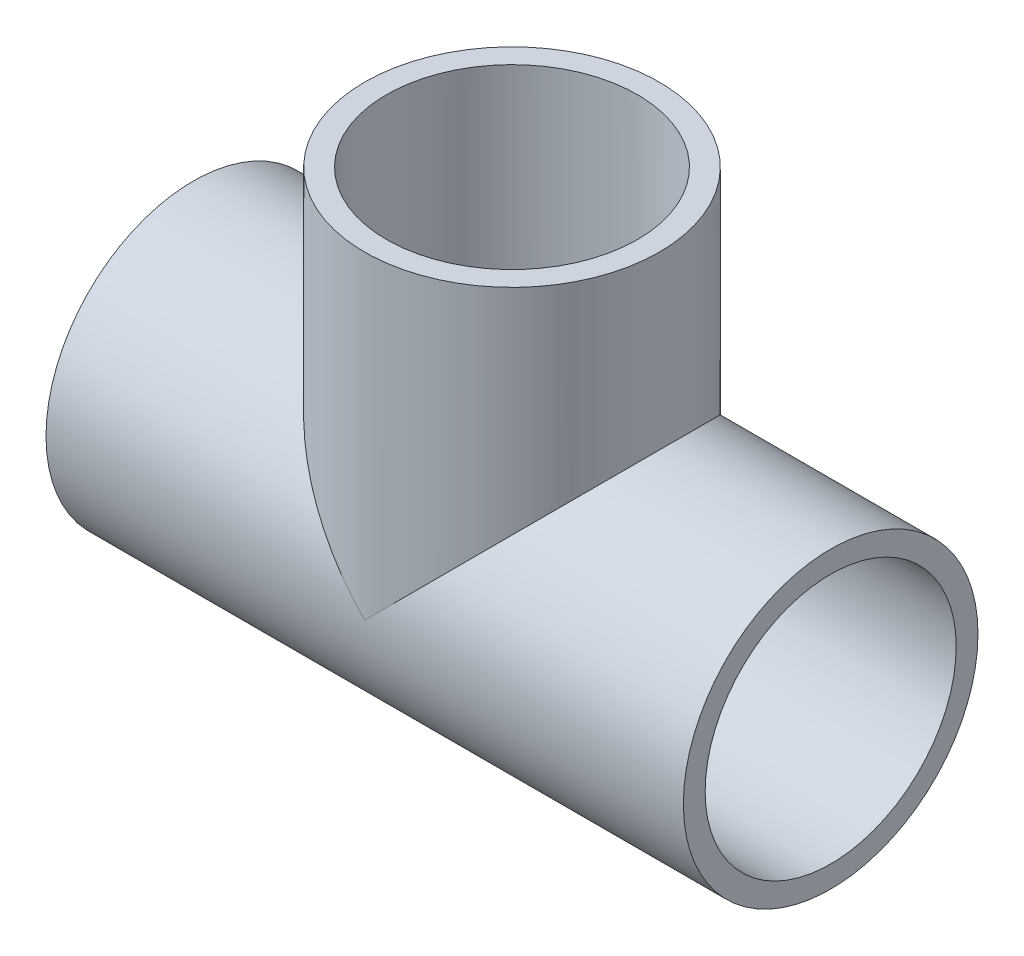
SolidWorks part; units mm, degrees
ref_plane "Front Plane" through (0, 0, 0) normal (0, 0, 1) x (1, 0, 0)
ref_plane "Top Plane" through (0, 0, 0) normal (0, 1, 0) x (1, 0, 0)
ref_plane "Right Plane" through (0, 0, 0) normal (1, 0, 0) x (0, 0, -1)
sketch "Sketch0" plane through (0, 0, 0) normal (0, 0, 1) x (1, 0, 0)
  line L0 (-53.848, 0) -> (0, 0) construction
  line L1 (0, 0) -> (0, 53.848) construction
  line L2 (-22.225, 0) -> (0, 0) construction
  line L3 (0, 0) -> (0, 22.225) construction
  line L4 (-53.848, 24.892) -> (-53.848, -24.892) construction
  line L5 (-22.225, 21.0185) -> (-53.848, 21.209) construction
  line L6 (-22.225, 21.0185) -> (-22.225, -21.0185) construction
  line L7 (-22.225, -21.0185) -> (-53.848, -21.209) construction
  line L8 (-53.848, 21.209) -> (-53.848, -21.209) construction
  line L9 (-24.892, 53.848) -> (24.892, 53.848) construction
  line L10 (-21.209, 53.848) -> (21.209, 53.848) construction
  line L11 (21.209, 53.848) -> (21.0185, 22.225) construction
  line L12 (21.0185, 22.225) -> (-21.0185, 22.225) construction
  line L13 (-21.0185, 22.225) -> (-21.209, 53.848) construction
  line L14 (-22.225, 17.526) -> (-22.225, -17.526) construction
  line L15 (-53.848, 0) -> (-22.225, 0) construction
  line L16 (0, 53.848) -> (0, 22.225) construction
  line L17 (0, 0) -> (22.225, 0) construction
  line L18 (-17.526, 22.225) -> (17.526, 22.225) construction
  line L19 (22.225, 0) -> (53.848, 0) construction
  dimension "H" = 53.848
  dimension "G" = 22.225
  dimension "M" = 49.784
  dimension "OD A" = 42.418
  dimension "OD B" = 42.037
  dimension "ID" = 35.052
  dimension "H3" = 53.848
sketch "Sketch1" plane through (0, 0, 0) normal (0, 0, 1) x (1, 0, 0)
  line L0 (-53.848, 0) -> (0, 0) construction
  line L1 (-53.848, 0) -> (0, 0) construction
  line L2 (0, 0) -> (0, -24.892) construction
  line L3 (-53.848, -24.892) -> (-22.225, -24.892)
  line L4 (-53.848, -24.892) -> (-53.848, -21.209)
  line L5 (-53.848, -21.209) -> (-22.225, -21.0185)
  line L6 (-22.225, -24.892) -> (-22.225, -21.0185)
  line L7 (-22.225, -24.892) -> (0, -24.892) construction
  line L8 (53.848, -21.209) -> (22.225, -21.0185)
  line L9 (53.848, -24.892) -> (53.848, -21.209)
  line L10 (22.225, -24.892) -> (22.225, -21.0185)
  line L11 (53.848, -24.892) -> (22.225, -24.892)
revolve "Revolve1" add sketch "Sketch1" angle 360 about L1
sketch "Sketch2" plane through (0, 0, 0) normal (0, 0, 1) x (1, 0, 0)
  line L0 (21.209, 53.848) -> (21.0185, 22.225)
  line L1 (21.0185, 22.225) -> (24.892, 22.225)
  line L2 (24.892, 22.225) -> (24.892, 53.848)
  line L3 (24.892, 53.848) -> (21.209, 53.848)
  line L4 (0, 0) -> (0, 53.848) construction
  line L5 (0, 0) -> (0, 53.848) construction
revolve "Revolve2" add sketch "Sketch2" angle 360 about L5
sketch "Sketch3" plane through (-22.225, 0, 0) normal (1, 0, 0) x (0, 0, -1)
  circle A0 centre (0, 0) radius 17.526
  circle A1 centre (0, 0) radius 24.892
sketch "Sketch4" plane through (-22.225, 0, 0) normal (1, 0, 0) x (0, 0, -1)
  circle A0 centre (0, 0) radius 24.892 construction
  circle A1 centre (0, 0) radius 24.892
extrude "Boss-Extrude1" add sketch "Sketch4" along normal up to vertex
sketch "Sketch5" plane through (0, 22.225, 0) normal (0, -1, 0) x (1, 0, 0)
  circle A0 centre (0, 0) radius 24.892 construction
  circle A1 centre (0, 0) radius 24.892
extrude "Boss-Extrude2" add sketch "Sketch5" along normal up to vertex (22.225 mm away) up to point (0, 0, 0)
sketch "Sketch6" plane through (0, 0, 0) normal (0, 0, 1) x (1, 0, 0)
  line L0 (-53.848, -21.209) -> (-22.225, -21.0185)
  line L1 (-22.225, -21.0185) -> (-22.225, -17.526)
  line L2 (-22.225, -17.526) -> (22.225, -17.526)
  line L3 (22.225, -21.0185) -> (22.225, 17.7797) construction
  line L4 (0, -17.526) -> (0, 0) construction
  line L5 (22.225, -21.0185) -> (22.225, -17.526)
  line L6 (53.848, -21.209) -> (53.848, 21.209) construction
  line L7 (53.848, -24.892) -> (53.848, 24.892) construction
  line L8 (53.848, -21.209) -> (53.848, 0)
  line L9 (53.848, 0) -> (-53.848, 0)
  line L10 (-53.848, 0) -> (-53.848, -21.209)
  line L11 (53.848, -21.209) -> (22.225, -21.0185)
revolve "Cut-Revolve1" cut sketch "Sketch6" angle 360 about L9
sketch "Sketch7" plane through (0, 0, 0) normal (0, 0, 1) x (1, 0, 0)
  line L0 (21.209, 53.848) -> (21.0185, 22.225)
  line L1 (21.0185, 22.225) -> (17.526, 22.225)
  line L2 (17.526, 22.225) -> (17.526, 0)
  line L3 (0, 0) -> (22.225, 0) construction
  line L4 (17.526, 0) -> (0, 0)
  line L5 (0, 0) -> (0, 53.848)
  line L6 (-24.892, 53.848) -> (24.892, 53.848) construction
  line L7 (0, 53.848) -> (21.209, 53.848)
revolve "Cut-Revolve2" cut sketch "Sketch7" angle 360 about L5
